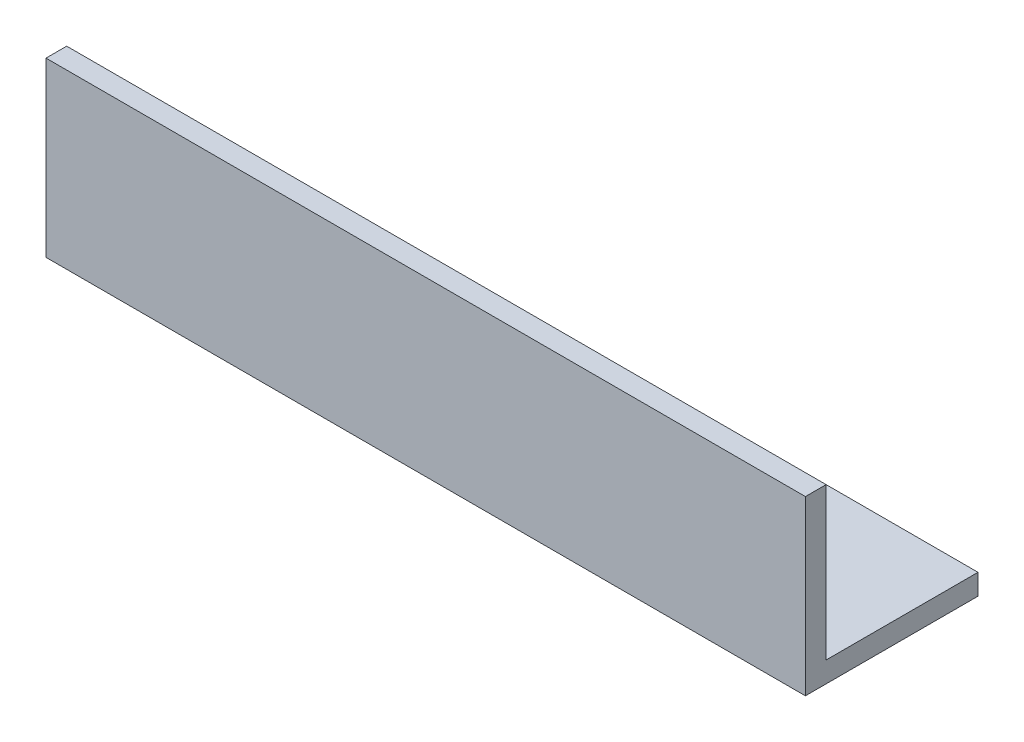
SolidWorks part; units mm, degrees
ref_plane "Спереди" through (0, 0, 0) normal (0, 0, 1) x (1, 0, 0)
ref_plane "Сверху" through (0, 0, 0) normal (0, 1, 0) x (1, 0, 0)
ref_plane "Справа" through (0, 0, 0) normal (1, 0, 0) x (0, 0, -1)
sketch "Эскиз1" plane through (0, 0, 0) normal (1, 0, 0) x (0, 0, -1)
  line L0 (0, 25) -> (0, 0)
  line L1 (0, 0) -> (25, 0)
  line L2 (25, 0) -> (25, 3)
  line L3 (25, 3) -> (3, 3)
  line L4 (3, 3) -> (3, 25)
  line L5 (3, 25) -> (0, 25)
extrude "Бобышка-Вытянуть1" add sketch "Эскиз1" along normal blind 110
